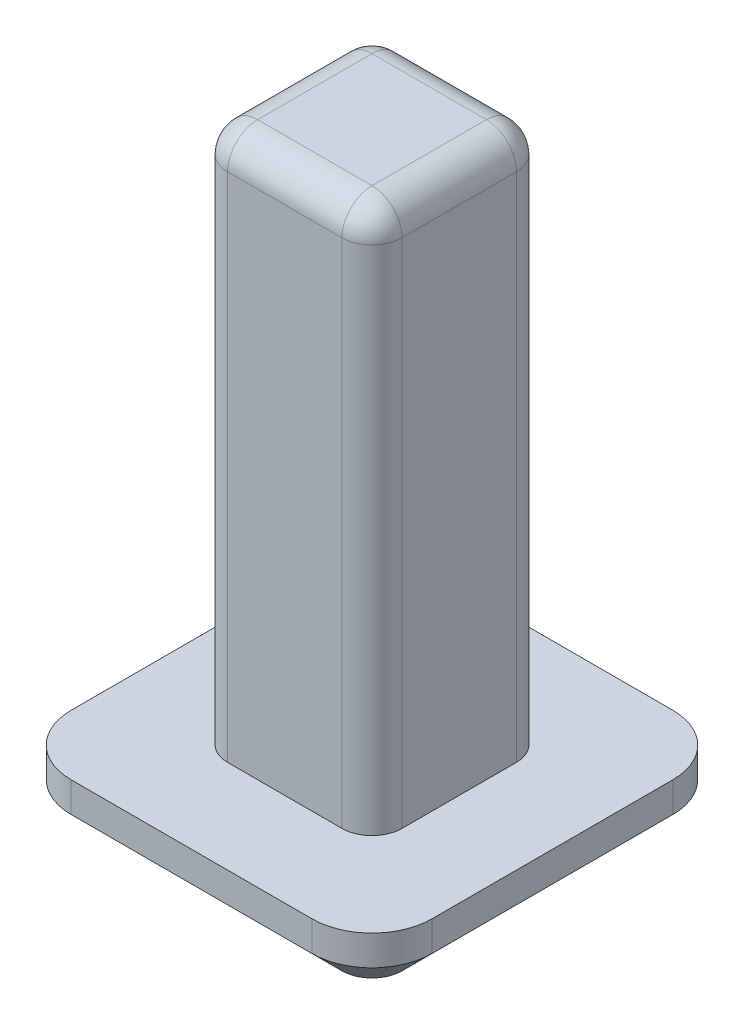
SolidWorks part; units mm, degrees
ref_plane "Front Plane" through (0, 0, 0) normal (0, 0, 1) x (1, 0, 0)
ref_plane "Top Plane" through (0, 0, 0) normal (0, 1, 0) x (1, 0, 0)
ref_plane "Right Plane" through (0, 0, 0) normal (1, 0, 0) x (0, 0, -1)
sketch "Sketch1" plane through (0, 0, 0) normal (0, 1, 0) x (1, 0, 0)
  line L1 (-3, -3) -> (3, -3)
  line L2 (-3, -3) -> (-3, 3)
  line L3 (-3, 3) -> (3, 3)
  line L4 (3, -3) -> (3, 3)
  line L5 (-3, -3) -> (3, 3) construction
  line L6 (-3, 3) -> (3, -3) construction
  point P0 (0, 0)
  dimension "D1" = 6
extrude "Boss-Extrude1" add sketch "Sketch1" along normal blind 1
fillet "Fillet1" radius 1 4 edges at (-3, 0.5, 3) (-3, 0.5, -3) (3, 0.5, -3) (3, 0.5, 3)
sketch "Sketch2" plane through (0, 1, 0) normal (0, 1, 0) x (1, 0, 0)
  line L1 (-1.45, -1.45) -> (1.45, -1.45)
  line L2 (-1.45, -1.45) -> (-1.45, 1.45)
  line L3 (-1.45, 1.45) -> (1.45, 1.45)
  line L4 (1.45, -1.45) -> (1.45, 1.45)
  line L5 (-1.45, -1.45) -> (1.45, 1.45) construction
  line L6 (-1.45, 1.45) -> (1.45, -1.45) construction
  circle A0 centre (0, 0) radius 1.45 construction
  dimension "D1" = 2.9
extrude "Boss-Extrude2" add sketch "Sketch2" along normal blind 9
fillet "Fillet2" radius 0.5 4 edges at (1.45, 5.5, -1.45) (-1.45, 5.5, -1.45) (1.45, 5.5, 1.45) (-1.45, 5.5, 1.45)
fillet "Fillet3" radius 0.5 8 edges at (-1.3036, 10, 1.3036) (-1.45, 10, 0) (-1.3036, 10, -1.3036) (0, 10, -1.45) (1.3036, 10, -1.3036) (1.45, 10, 0) (1.3036, 10, 1.3036) (0, 10, 1.45)
chamfer "Chamfer1" distance 0.5 angle 45 8 edges at (0, 0, -3) (-2.7071, 0, -2.7071) (2.7071, 0, -2.7071) (-3, 0, 0) (3, 0, 0) (-2.7071, 0, 2.7071) (2.7071, 0, 2.7071) (0, 0, 3)
